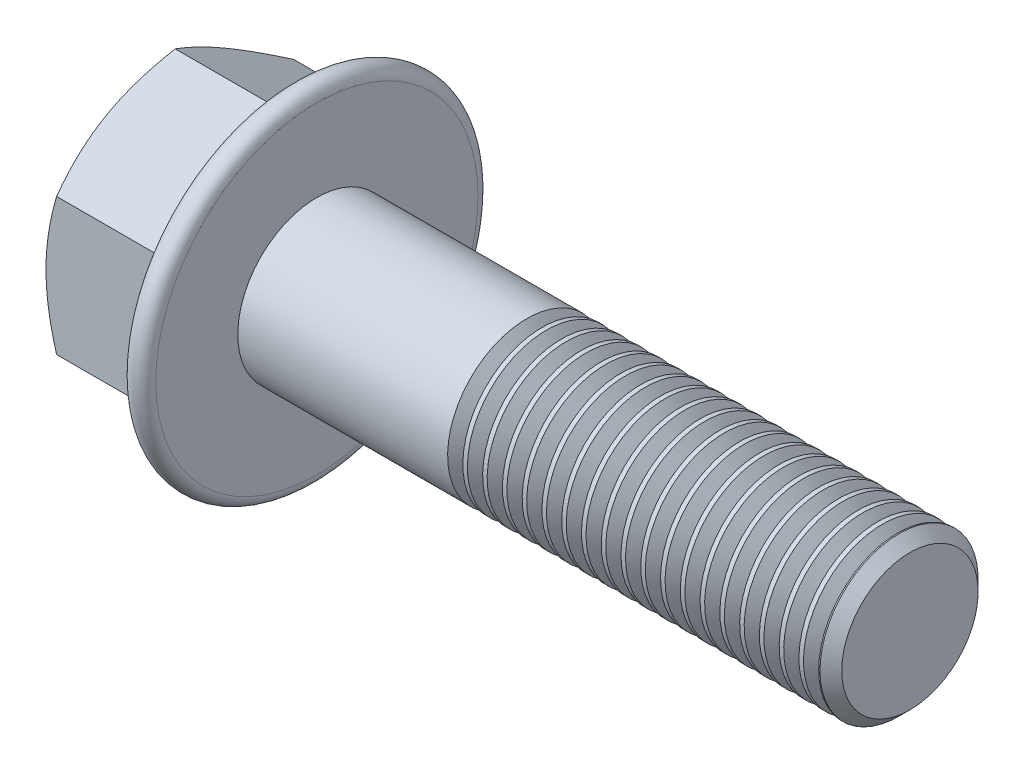
SolidWorks part; units mm, degrees
extrude "BaseHead" add sketch "Sketch1" along normal blind 15.4
sketch "Sketch1" plane through (0, 0, 0) normal (1, 0, 0) x (0, 0, -1)
  line L0 (12, 6.9282) -> (12, -6.9282)
  line L1 (-12, 6.9282) -> (-12, -6.9282)
  line L2 (12, -6.9282) -> (0, -13.8564)
  line L3 (0, -13.8564) -> (-12, -6.9282)
  line L4 (12, 6.9282) -> (0, 13.8564)
  line L5 (0, 13.8564) -> (-12, 6.9282)
  dimension "Width_flats" = 24
  dimension "D2" = 120
  dimension "D3" = 12
  dimension "D4" = 12
  dimension "D5" = 12
ref_plane "Plane1" through (0, 0, 0) normal (0, 0, 1) x (1, 0, 0)
ref_plane "Plane2" through (0, 0, 0) normal (0, 1, 0) x (1, 0, 0)
ref_plane "Plane3" through (0, 0, 0) normal (1, 0, 0) x (0, 0, -1)
sketch "BodySke" plane through (0, 0, 0) normal (0, 0, 1) x (1, 0, 0)
  line L0 (0, 6.9282) -> (0, -6.9282) construction
  line L1 (0, 0) -> (75.4, 0)
  line L2 (0, 0) -> (0, 8)
  line L3 (0, 8) -> (74.2985, 8)
  line L4 (75.4, 0) -> (75.4, 6.8985)
  line L5 (15.4, 13.8564) -> (15.4, 6.9282) construction
  line L6 (75.4, 6.8985) -> (74.2985, 8)
  line L7 (0, 0) -> (96.52, 0) construction
  line L8 (75.4, -6.8985) -> (74.2985, -8) construction
  line L9 (0, -8) -> (74.2985, -8) construction
  line L10 (17.4, 15.24) -> (17.4, -1.27) construction
  line L11 (37.4, 15.24) -> (37.4, -1.27) construction
  line L12 (15.4, 6.9282) -> (15.4, -6.9282) construction
  dimension "Diameter" = 16
  dimension "Advance" = 2
revolve "BaseBody" add sketch "BodySke"
cosmetic thread "ThreadCosmetic" [suppressed]
fillet "HeadFillet" [suppressed] radius 0.6
sketch "Sketch3" plane through (0, 0, 0) normal (0, 0, 1) x (1, 0, 0)
  line L0 (0, 12) -> (3.9585, 18.8564)
  line L1 (0, 13.8564) -> (0, 6.9282) construction
  line L2 (3.9585, 18.8564) -> (3.9585, 23.8564)
  line L3 (3.9585, 23.8564) -> (-10, 23.8564)
  line L4 (-10, 23.8564) -> (-10, 12)
  line L5 (-10, 12) -> (0, 12)
  line L6 (0, 0) -> (99.06, 0) construction
  line L7 (15.4, 13.8564) -> (0, 13.8564) construction
  dimension "D1" = 12
  dimension "D2" = 5
  dimension "D3" = 10
  dimension "D4" = 5
  dimension "Head_ch_ang" = 30
revolve "HeadChamfer" cut sketch "Sketch3" angle 360 about L6
sketch "Sketch4" plane through (0, 0, 0) normal (0, 0, 1) x (1, 0, 0)
  line L0 (6.9903, 0) -> (13.0724, 16.7104)
  line L1 (15.4, 13.8564) -> (15.4, 6.9282) construction
  line L2 (13, 34.3444) -> (13, 16.9779) construction
  line L3 (15.4, 0) -> (15.4, 16.3)
  line L4 (8.3021, 17.5) -> (20.1618, 17.5) construction
  line L5 (0, 0) -> (95.25, 0) construction
  line L6 (0, 0) -> (96.52, 0) construction
  line L7 (6.9903, 0) -> (15.4, 0)
  line L8 (8.3021, -17.5) -> (20.1618, -17.5) construction
  arc A0 (15.4, 16.3) -> (13.0724, 16.7104) centre (14.2, 16.3) ccw
  dimension "D1" = 20
  dimension "Flange_thickness" = 2.4
  dimension "Flange_dia" = 35
revolve "Flange" add sketch "Sketch4" angle 360 about L5
fillet "FlangeHexFillet" radius 1 6 edges
sketch "ThdSchSke" plane through (0, 0, 0) normal (0, 0, 1) x (1, 0, 0)
  line L0 (37.4, -6.8985) -> (36.6287, -8)
  line L1 (37.4, -6.8985) -> (38.1713, -8)
  line L2 (38.1713, -8) -> (38.1713, -10)
  line L3 (-3.175, 0) -> (5.1513, 0) construction
  line L5 (38.1713, -10) -> (36.6287, -10)
  line L6 (36.6287, -10) -> (36.6287, -8)
  dimension "Thread_minor" = 13.797
  dimension "Diameter" = 16
  dimension "Start" = 37.4
revolve "ThreadSchematic" cut sketch "ThdSchSke" angle 360 about L3
pattern_linear "ThdSchPat" count 19 spacing 2 along (1, 0, 0) of "ThreadSchematic"
equation "\"D3@Sketch1\" = \"Width_flats@Sketch1\" / 2"
equation "\"D4@Sketch1\" = \"D3@Sketch1\""
equation "\"D5@Sketch1\" = \"D4@Sketch1\""
equation "\"Thread_minor@ThreadCosmetic\" = \"Minor_dia@BodySke\""
equation "\"D1@Sketch3\" = \"Width_flats@Sketch1\" / 2"
equation "\"Thread_length@ThreadCosmetic\" = ((sgn( (\"Length@BodySke\" - \"Advance@BodySke\" ) - \"Thread_nom@BodySke\" )-1)*( (\"Length@BodySke\" - \"Advance@BodySke\" ) - \"Thread_nom@BodySke\" ))/-2+ \"Thread_nom@BodySke\""
equation "\"Thread_minor@ThdSchSke\" = \"Minor_dia@BodySke\""
equation "\"Diameter@ThdSchSke\" = \"Diameter@BodySke\""
equation "\"Overcut@ThdSchSke\" = \"Diameter@BodySke\" * 1.25"
equation "\"Start@ThdSchSke\" = \"Head_ht@BaseHead\" + \"Length@BodySke\" - \"Thread_length@ThreadCosmetic\"  '---Non-countersunk---"
equation "\"Num_threads@ThdSchPat\" = int( \"Thread_length@ThreadCosmetic\" / \"Advance@BodySke\" + 0.999 )  + 1"
equation "\"Advance@ThdSchPat\" = \"Thread_length@ThreadCosmetic\" /  (\"Num_threads@ThdSchPat\" - 1) 'relax it"
equation "\"Num_threads@ThdSchPat\" = \"Num_threads@ThdSchPat\" - sgn( \"Num_threads@ThdSchPat\" - 1) '---chamfered tips only---"
